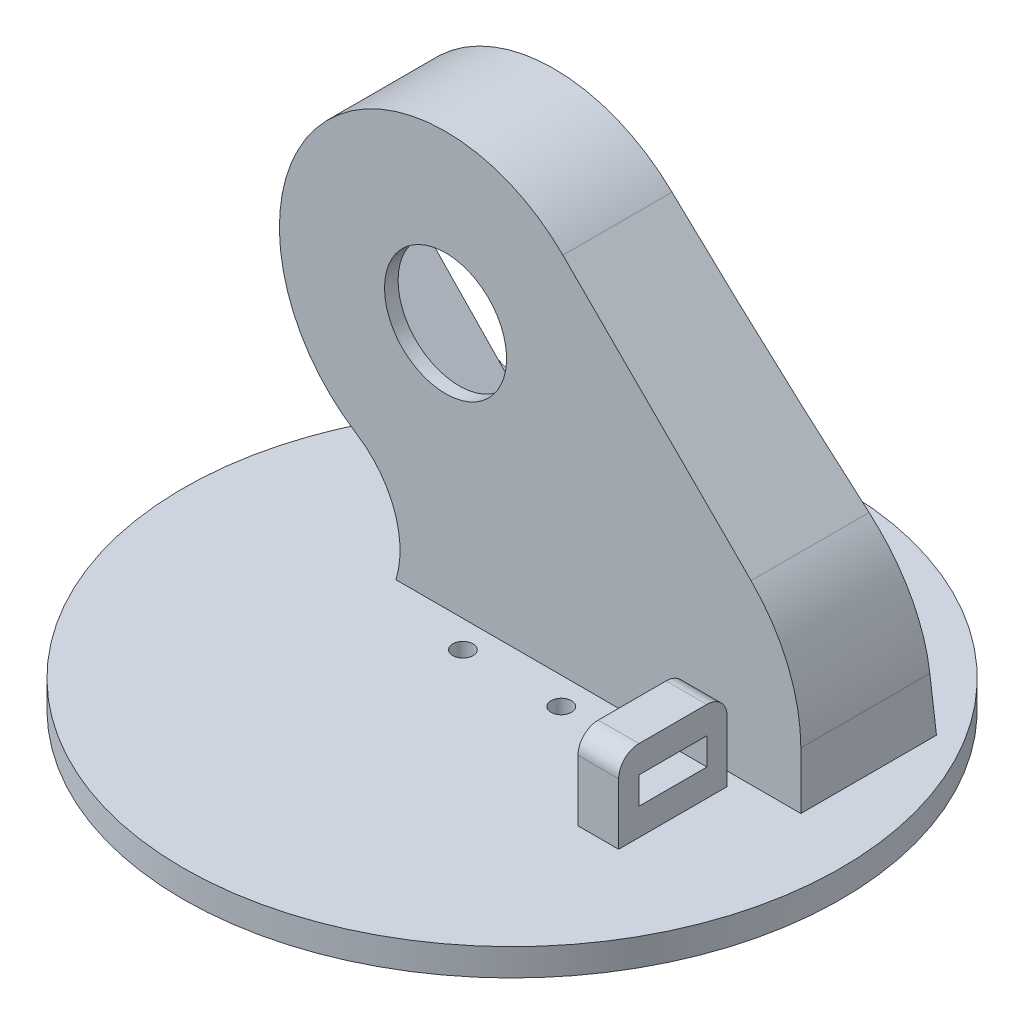
SolidWorks part; units mm, degrees
ref_plane "Ön Düzlem" through (0, 0, 0) normal (0, 0, 1) x (1, 0, 0)
ref_plane "Üst Düzlem" through (0, 0, 0) normal (0, 1, 0) x (1, 0, 0)
ref_plane "Sağ Düzlem" through (0, 0, 0) normal (1, 0, 0) x (0, 0, -1)
sketch "Çizim2" plane through (0, 0, 0) normal (0, 1, 0) x (1, 0, 0)
  line L0 (0, -55) -> (0, 55) construction
  circle A0 centre (0, -4) radius 48.5
  circle A1 centre (7.25, -4) radius 1.5
  circle A2 centre (-7.25, -4) radius 1.5
  point P11 (-3.8355, -5.4644)
  dimension "D1" = 97
  dimension "D5" = 3
  dimension "D6" = 3
  dimension "D2" = 4
  dimension "D3" = 7.25
  dimension "D4" = 14.5
extrude "Yükseklik-Ekstrüzyon1" add sketch "Çizim2" against normal blind 4
sketch "Çizim3" plane through (0, 0, 0) normal (0, 0, 1) x (1, 0, 0)
  line L5 (3.4959, 53.7552) -> (31.2389, 26.0713)
  line L6 (-22.1448, 0) -> (38.5801, 0)
  line L7 (53.35, 0) -> (-53.35, 0) construction
  line L8 (38.5801, 8.3748) -> (38.5801, 0)
  line L13 (-21.1189, 0) -> (-8.8605, 0)
  arc A2 (3.4959, 53.7552) -> (-26.9439, 15.7307) centre (-13.8097, 36.4126) ccw
  arc A7 (38.5801, 8.3748) -> (31.2389, 26.0713) centre (13.5801, 8.3748) ccw
  arc A9 (-21.1189, 0) -> (-26.9439, 15.7307) centre (-34.3701, 4.0369) ccw
  dimension "D3" = 49
  dimension "D20" = 50
extrude "Yükseklik-Ekstrüzyon2" add sketch "Çizim3" against normal blind 20 contours A9 L6 L8 A7 L5 A2
ref_plane "Düzlem1" through (0, 0, -20) normal (0, 0, -1) x (-1, 0, 0)
sketch "Çizim5" plane through (0, 0, -20) normal (0, 0, -1) x (-1, 0, 0)
  line L0 (-29.5801, 0) -> (-29.5801, 8.3558)
  line L1 (-29.5801, 0) -> (11.1189, 0)
  line L2 (0, 52.8912) -> (-16.7292, 34.7238)
  arc A5 (-17.5885, 33.6512) -> (-16.7292, 34.7238) centre (-9.373, 27.9499) cw
  arc A6 (-29.5801, 8.3558) -> (-28.9606, 11.8207) centre (-19.5801, 8.3558) cw
  arc A7 (-28.9606, 11.8207) -> (-17.5885, 33.6512) centre (62.609, -22.0033) cw
  arc A8 (11.1189, 0) -> (22.1426, 16.5931) centre (29.1189, 0) cw
  arc A9 (0, 52.8912) -> (22.1426, 16.5931) centre (13.8097, 36.4126) cw
extrude "Kes-Ekstrüzyon2" cut sketch "Çizim5" against normal blind 9
sketch "Çizim7" plane through (0, 0, -20) normal (0, 0, -1) x (-1, 0, 0)
  line L5 (28.4831, 36.4909) -> (0, 7)
  line L6 (0, 7) -> (-15.1051, 21.5889)
  line L7 (13.3779, 51.0798) -> (-15.1051, 21.5889)
  line L8 (28.4831, 36.4909) -> (13.3779, 51.0798)
extrude "Kes-Ekstrüzyon4" cut sketch "Çizim7" against normal blind 18
sketch "Çizim8" plane through (0, 0, -20) normal (0, 0, -1) x (-1, 0, 0)
  circle A1 centre (13.8097, 36.4126) radius 8.9994
extrude "Kes-Ekstrüzyon6" cut sketch "Çizim8" against normal blind 20
sketch "Çizim10" plane through (0, 0, -20) normal (0, 0, -1) x (-1, 0, 0)
  circle A4 centre (-13.5801, 15.2501) radius 1.3
  circle A5 centre (-6.3186, 8.3748) radius 1.3
  circle A6 centre (19.7659, 49.7761) radius 1.3
  circle A7 centre (27.0274, 42.9008) radius 1.3
extrude "Kes-Ekstrüzyon7" cut sketch "Çizim10" against normal blind 13
sketch3d "3B Çizim1"
  line L2 (29.7143, 0, 2) -> (29.7143, 0, 18)
  line L3 (29.7143, 0, 2) -> (23.7143, 0, 2)
  line L4 (23.7143, 0, 2) -> (23.7143, 0, 18)
  line L5 (29.7143, 0, 18) -> (23.7143, 0, 18)
  dimension "D1" = 16
  dimension "D2" = 6
  dimension "D3" = 2
extrude "Yükseklik-Ekstrüzyon3" add sketch "3B Çizim1" along direction (0, 1, 0) on the side of the normal blind 12
fillet "Radyus1" radius 3 1 edges
fillet "Radyus2" radius 3 1 edges
ref_plane "Düzlem2" through (29.7143, 0, 0) normal (1, 0, 0) x (0, 0, -1)
sketch "Çizim11" plane through (29.7143, 0, 0) normal (1, 0, 0) x (0, 0, -1)
  line L0 (-15, 12) -> (-5, 12) construction
  line L1 (-14.98, 8) -> (-4.98, 8)
  line L2 (-14.98, 8) -> (-14.98, 4)
  line L3 (-14.98, 4) -> (-4.98, 4)
  line L4 (-4.98, 8) -> (-4.98, 4)
  dimension "D1" = 4
  dimension "D2" = 4
extrude "Kes-Ekstrüzyon8" cut sketch "Çizim11" against normal blind 6
ref_plane "Düzlem3" through (0, -4, 0) normal (0, -1, 0) x (-1, 0, 0)
sketch "Çizim12" plane through (0, -4, 0) normal (0, -1, 0) x (-1, 0, 0)
  circle A0 centre (0.0711, -4) radius 4.0006
  point P6 (0, 0)
extrude "Kes-Ekstrüzyon9" cut sketch "Çizim12" against normal blind 2
sketch "Çizim13" plane through (0, 0, 0) normal (1, 0, 0) x (0, 0, -1)
  line L0 (16, 60.9126) -> (25.8775, 60.9126)
  line L1 (53.35, 0) -> (-53.35, 0) construction
  line L2 (20, -33.502) -> (20, 33.502) construction
  line L3 (20, 60.9126) -> (0, 60.9126) construction
  line L4 (25.8775, 60.9126) -> (25.8775, 0)
  line L5 (25.8775, 0) -> (20, 0)
  spline S0 degree 2 poles (16, 60.9126) (16.196, 30.3417) (20, 0) knots 0 0 0 1 1 1
  dimension "D1" = 4
extrude "Kes-Ekstrüzyon10" cut sketch "Çizim13" against normal blind 40 and the other way blind 40
